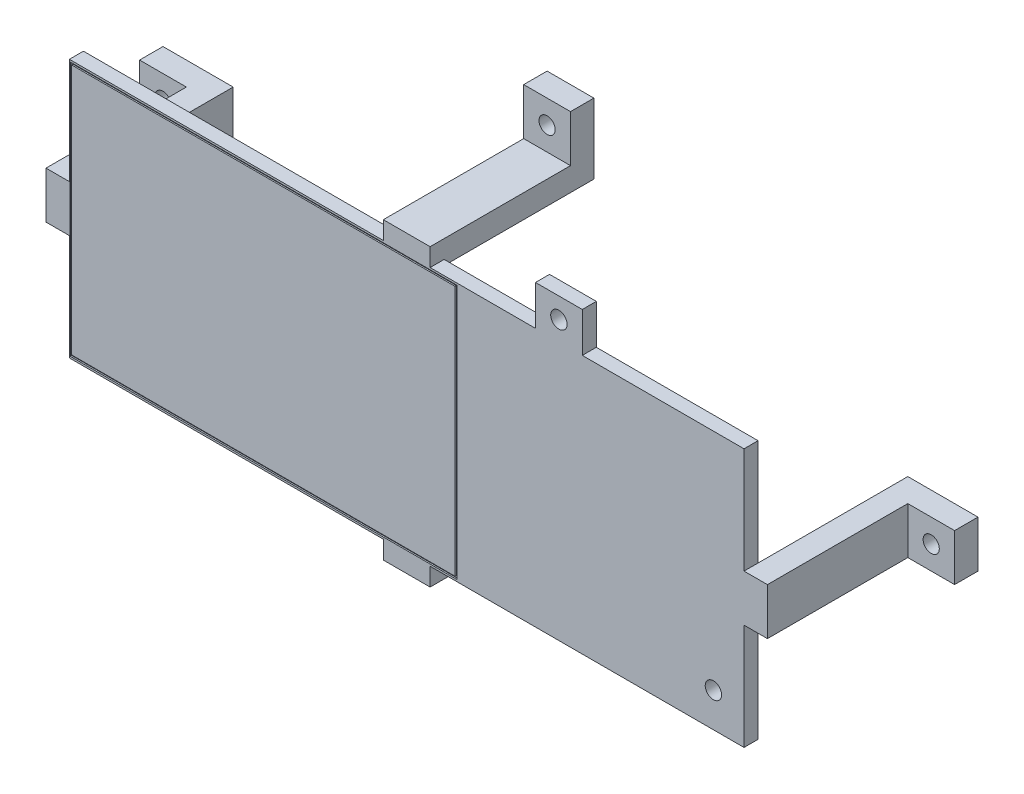
SolidWorks part; units mm, degrees
ref_plane "Front Plane" through (0, 0, 0) normal (0, 0, 1) x (1, 0, 0)
ref_plane "Top Plane" through (0, 0, 0) normal (0, 1, 0) x (1, 0, 0)
ref_plane "Right Plane" through (0, 0, 0) normal (1, 0, 0) x (0, 0, -1)
sketch "Sketch2" plane through (0, 0, 0) normal (0, 0, 1) x (1, 0, 0)
  line L0 (-68.085, -22.5) -> (68.085, 22.5) construction
  line L1 (-68.085, 22.5) -> (68.085, 22.5) construction
  line L2 (-68.085, 22.5) -> (-68.085, -22.5) construction
  line L3 (-68.085, -22.5) -> (68.085, -22.5) construction
  line L4 (68.085, 22.5) -> (68.085, -22.5) construction
  line L5 (-72.085, 26.5) -> (72.085, 26.5) construction
  line L6 (72.085, 26.5) -> (72.085, -26.5) construction
  line L7 (-72.085, -26.5) -> (72.085, -26.5) construction
  line L8 (-72.085, 26.5) -> (-72.085, -26.5) construction
  line L9 (0, 0) -> (-100, 0) construction
  line L10 (-77.085, 5) -> (-72.085, 5)
  line L11 (-77.085, 5) -> (-77.085, -5)
  line L12 (-77.085, -5) -> (-72.085, -5)
  line L13 (-72.085, 5) -> (-72.085, -5)
  line L14 (-5, 31.5) -> (5, 31.5)
  line L15 (-5, 31.5) -> (-5, 26.5)
  line L16 (-5, 26.5) -> (5, 26.5)
  line L17 (5, 31.5) -> (5, 26.5)
  line L18 (0, 0) -> (0, 108.7377) construction
  line L19 (-77.085, 5) -> (-72.085, -5) construction
  line L20 (-5, 26.5) -> (5, 31.5) construction
  line L21 (77.085, -5) -> (72.085, -5)
  line L22 (77.085, 5) -> (77.085, -5)
  line L23 (72.085, 5) -> (72.085, -5)
  line L24 (77.085, 5) -> (72.085, 5)
  line L25 (-5, -26.5) -> (5, -26.5)
  line L26 (-5, -31.5) -> (-5, -26.5)
  line L27 (-5, -31.5) -> (5, -31.5)
  line L28 (5, -31.5) -> (5, -26.5)
  point P4 (0, 0)
  point P23 (-74.585, 0)
  point P25 (0, 29)
  dimension "D1" = 45
  dimension "D2" = 136.17
  dimension "D4" = 5
  dimension "D5" = 10
  dimension "D6" = 5
  dimension "D7" = 10
  dimension "D3" = 4
extrude "Boss-Extrude1" add sketch "Sketch2" along normal blind 32
sketch "Sketch3" plane through (0, 0, 32) normal (0, 0, 1) x (1, 0, 0)
  line L0 (-82.5, 27.64) -> (82.5, -27.64) construction
  line L1 (-82.5, 27.64) -> (82.5, 27.64)
  line L2 (-82.5, 27.64) -> (-82.5, -27.64)
  line L3 (-82.5, -27.64) -> (82.5, -27.64)
  line L4 (82.5, 27.64) -> (82.5, -27.64)
  point P4 (0, 0)
  dimension "D1" = 165
  dimension "D2" = 55.28
extrude "Boss-Extrude2" add sketch "Sketch3" along normal blind 3
sketch "Sketch4" plane through (0, 0, 32) normal (0, 0, 1) x (1, 0, 0)
  line L0 (-5, 27.64) -> (5, 27.64) construction
  line L1 (5, 27.64) -> (5, 31.5) construction
  line L2 (5, 31.5) -> (-5, 31.5) construction
  line L3 (-5, 31.5) -> (-5, 27.64) construction
  line L4 (5, -31.5) -> (5, -27.64) construction
  line L5 (5, -27.64) -> (-5, -27.64) construction
  line L6 (-5, -27.64) -> (-5, -31.5) construction
  line L7 (-5, -31.5) -> (5, -31.5) construction
  line L8 (-5, 27.64) -> (5, 27.64)
  line L9 (5, 27.64) -> (5, 31.5)
  line L10 (5, 31.5) -> (-5, 31.5)
  line L11 (-5, 31.5) -> (-5, 27.64)
  line L12 (5, -31.5) -> (5, -27.64)
  line L13 (5, -27.64) -> (-5, -27.64)
  line L14 (-5, -27.64) -> (-5, -31.5)
  line L15 (-5, -31.5) -> (5, -31.5)
extrude "Boss-Extrude3" add sketch "Sketch4" along normal up to surface (3 mm away) up to face at (0, 0, 35)
sketch "Sketch5" plane through (0, 5, 0) normal (0, 1, 0) x (1, 0, 0)
  line L0 (0, 0) -> (0, -40.7206) construction
  line L1 (-77.085, 0) -> (-87.085, 0)
  line L2 (-77.085, 0) -> (-77.085, -5)
  line L3 (-77.085, -5) -> (-87.085, -5)
  line L4 (-87.085, 0) -> (-87.085, -5)
  line L5 (87.085, 0) -> (87.085, -5)
  line L6 (77.085, 0) -> (87.085, 0)
  line L7 (77.085, 0) -> (77.085, -5)
  line L8 (77.085, -5) -> (87.085, -5)
  dimension "D1" = 5
  dimension "D2" = 10
extrude "Boss-Extrude4" add sketch "Sketch5" against normal up to surface (10 mm away) up to face at (-74.585, -5, 16)
sketch "Sketch7" plane through (-5, 0, 0) normal (-1, 0, 0) x (0, 0, 1)
  line L0 (0, 0) -> (45.7182, 0) construction
  line L1 (0, 31.5) -> (5, 31.5)
  line L2 (0, 31.5) -> (0, 41.5)
  line L3 (0, 41.5) -> (5, 41.5)
  line L4 (5, 31.5) -> (5, 41.5)
  line L5 (0, -41.5) -> (5, -41.5)
  line L6 (0, -31.5) -> (0, -41.5)
  line L7 (0, -31.5) -> (5, -31.5)
  line L8 (5, -31.5) -> (5, -41.5)
  dimension "D1" = 5
  dimension "D2" = 10
extrude "Boss-Extrude5" add sketch "Sketch7" against normal up to surface (10 mm away) up to face at (5, -28.5467, 22.3333)
sketch "Sketch8" plane through (0, 0, 5) normal (0, 0, 1) x (1, 0, 0)
  line L0 (-87.085, 5) -> (-77.085, -5) construction
  line L1 (-5, -31.5) -> (5, -41.5) construction
  line L2 (0, 0) -> (0, 49.5906) construction
  line L3 (0, 0) -> (57.6811, 0) construction
  circle A0 centre (-82.085, 0) radius 1.73
  circle A1 centre (0, -36.5) radius 1.73
  circle A2 centre (82.085, 0) radius 1.73
  circle A3 centre (0, 36.5) radius 1.73
  dimension "D1" = 3.46
  dimension "D2" = 3.46
extrude "Cut-Extrude1" cut sketch "Sketch8" against normal through all
sketch "Metro Express Layout Reference" plane through (0, 0, 35) normal (0, 0, 1) x (1, 0, 0)
  line L0 (0.32, 27.64) -> (0.32, -27.64) construction
  line L1 (14.74, 34.29) -> (68.08, 34.29) construction
  line L2 (14.74, 34.29) -> (14.74, -34.29) construction
  line L3 (14.74, -34.29) -> (68.08, -34.29) construction
  line L4 (68.08, 34.29) -> (68.08, -34.29) construction
  line L5 (82.5, -27.64) -> (82.5, 27.64) construction
  line L7 (-5, 27.64) -> (-82.5, 27.64) construction
  line L8 (-82.5, -27.64) -> (-5, -27.64) construction
  line L9 (-82.5, 27.64) -> (-82.5, -27.64) construction
  circle A0 centre (32.52, 31.75) radius 1.75 construction
  circle A1 centre (65.54, -20.32) radius 1.75 construction
  point P4 (68.08, 0)
  point P7 (82.5, 0)
  dimension "D5" = 3.5
  dimension "D7" = 3.5
  dimension "D1" = 68.58
  dimension "D2" = 53.34
  dimension "D3" = 17.78
  dimension "D4" = 2.54
  dimension "D6" = 13.97
  dimension "D8" = 2.54
  dimension "D9" = 82.82
  dimension "D10" = 14.42
sketch "Sketch10" plane through (0, 0, 35) normal (0, 0, 1) x (1, 0, 0)
  line L0 (82.5, 27.64) -> (5, 27.64) construction
  line L1 (27.52, 27.64) -> (37.52, 27.64)
  line L2 (27.52, 27.64) -> (27.52, 36.14)
  line L3 (27.52, 36.14) -> (37.52, 36.14)
  line L4 (37.52, 27.64) -> (37.52, 36.14)
  line L5 (68.08, 34.29) -> (68.08, -34.29) construction
  line L6 (68.08, -15.32) -> (69.93, -15.32)
  line L7 (68.08, -15.32) -> (68.08, -25.32)
  line L8 (68.08, -25.32) -> (69.93, -25.32)
  line L9 (69.93, -15.32) -> (69.93, -25.32)
  point P6 (32.52, 27.64)
  point P14 (68.08, -20.32)
  dimension "D1" = 8.5
  dimension "D2" = 10
  dimension "D3" = 10
  dimension "D4" = 4.39
extrude "Boss-Extrude6" add sketch "Sketch10" against normal up to surface (3 mm away) up to face at (74.585, 0, 32)
sketch "Sketch11" plane through (0, 0, 35) normal (0, 0, 1) x (1, 0, 0)
  circle A0 centre (32.52, 31.75) radius 1.75
  circle A1 centre (65.54, -20.32) radius 1.75
  circle A2 centre (32.52, 31.75) radius 1.75 construction
  circle A3 centre (65.54, -20.32) radius 1.75 construction
extrude "Cut-Extrude3" cut sketch "Sketch11" against normal through all
sketch "Sketch12" plane through (0, 0, 35) normal (0, 0, 1) x (1, 0, 0)
  line L0 (-82.5, 27.64) -> (-82.5, -27.64) construction
  line L1 (-71.785, 27.03) -> (10.535, 27.03) construction
  line L2 (-71.785, 27.03) -> (-71.785, -27.03) construction
  line L3 (-71.785, -27.03) -> (10.535, -27.03) construction
  line L4 (10.535, 27.03) -> (10.535, -27.03) construction
  line L5 (-71.985, 27.23) -> (-71.985, -27.23)
  line L6 (-12.815, 8.88) -> (12.815, 8.88) construction
  line L7 (-12.815, 8.88) -> (-12.815, -8.88) construction
  line L8 (-12.815, -8.88) -> (12.815, -8.88) construction
  line L9 (12.815, 8.88) -> (12.815, -8.88) construction
  line L10 (-71.985, -27.23) -> (10.735, -27.23)
  line L11 (10.735, 27.23) -> (10.735, -27.23)
  line L12 (-71.985, 27.23) -> (10.735, 27.23)
  line L13 (-71.585, 26.83) -> (-71.585, -26.83)
  line L14 (-71.585, -26.83) -> (10.335, -26.83)
  line L15 (10.335, 26.83) -> (10.335, -26.83)
  line L16 (-71.585, 26.83) -> (10.335, 26.83)
  point P4 (12.815, 0)
  point P5 (-71.785, 0)
  point P8 (-82.5, 0)
  point P15 (0, 8.88)
  dimension "D1" = 82.32
  dimension "D2" = 54.06
  dimension "D3" = 25.63
  dimension "D4" = 17.76
  dimension "D5" = 2.28
  dimension "D6" = 0.2
  dimension "D7" = 0.2
extrude "Cut-Extrude4" cut sketch "Sketch12" against normal blind 0.28
sketch "Sketch13" plane through (0, 0, 32) normal (0, 0, -1) x (-1, 0, 0)
  line L0 (82.5, -27.64) -> (82.5, 27.64)
  line L5 (-82.5, 27.64) -> (-82.5, -27.64)
  line L17 (-82.5, 27.64) -> (-37.52, 27.64) construction
  line L18 (-82.5, -27.64) -> (-72.085, -27.64)
  line L20 (-77.085, -5) -> (-72.085, -5)
  line L21 (-72.085, -27.64) -> (-72.085, -5)
  line L25 (-77.085, -5) -> (-77.085, 5)
  line L26 (-77.085, 5) -> (-72.085, 5)
  line L28 (-82.5, 27.64) -> (-72.085, 27.64)
  line L29 (-72.085, 5) -> (-72.085, 27.64)
  line L30 (5, 27.64) -> (82.5, 27.64) construction
  line L31 (82.5, -27.64) -> (72.085, -27.64)
  line L33 (77.085, -5) -> (72.085, -5)
  line L34 (72.085, -27.64) -> (72.085, -5)
  line L38 (77.085, -5) -> (77.085, 5)
  line L39 (77.085, 5) -> (72.085, 5)
  line L41 (82.5, 27.64) -> (72.085, 27.64)
  line L42 (72.085, 5) -> (72.085, 27.64)
  point P2 (-80.8007, -17.4238)
  point P4 (-81.9481, -25.4606)
extrude "Cut-Extrude5" cut sketch "Sketch13" against normal through all
